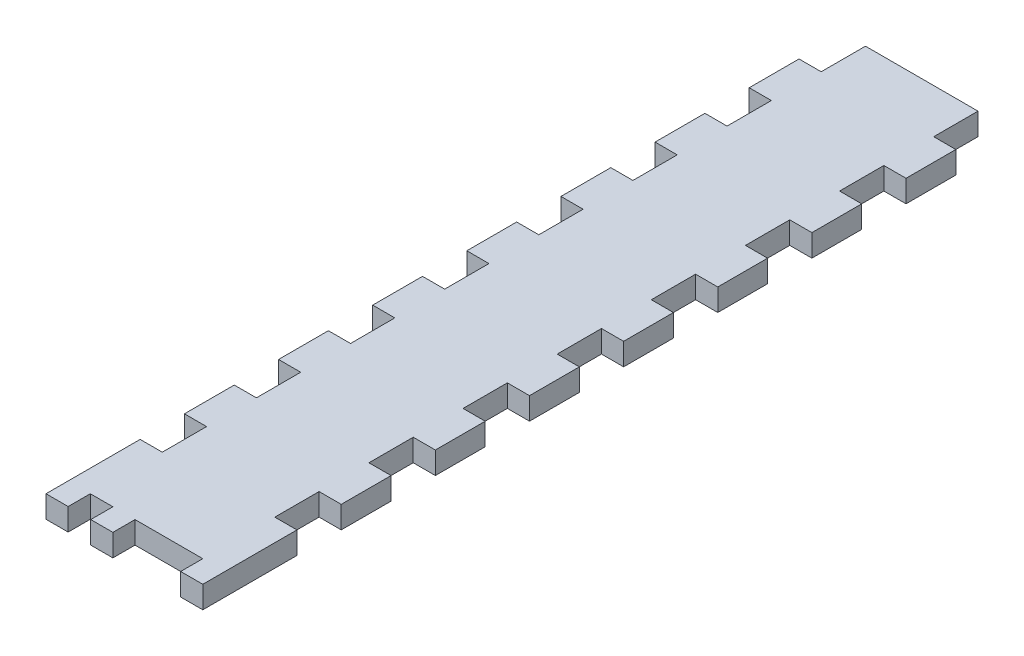
SolidWorks part; units mm, degrees
material "Acrylic (Medium-high impact)"
ref_plane "Front" through (0, 0, 0) normal (0, 0, 1) x (1, 0, 0)
ref_plane "Top" through (0, 0, 0) normal (0, 1, 0) x (1, 0, 0)
ref_plane "Right" through (0, 0, 0) normal (1, 0, 0) x (0, 0, -1)
sketch "Sketch1" plane through (0, 0, 0) normal (0, 0, 1) x (1, 0, 0)
  line L0 (0, 143.002) -> (0, -143.002) construction
  line L1 (-3.302, 133.858) -> (-3.302, -143.002)
  line L2 (-3.302, -143.002) -> (3.302, -143.002)
  line L3 (3.302, 143.002) -> (3.302, -143.002)
  line L4 (3.302, 143.002) -> (-16.256, 143.002)
  line L5 (-5.842, 136.398) -> (-16.256, 136.398)
  line L6 (-16.256, 143.002) -> (-16.256, 136.398)
  line L8 (-28.956, 155.448) -> (16.002, 155.448)
  line L9 (-28.956, 155.448) -> (-28.956, -149.352)
  line L10 (-28.956, -149.352) -> (16.002, -149.352)
  line L11 (16.002, 155.448) -> (16.002, -149.352)
  arc A0 (-3.302, 133.858) -> (-5.842, 136.398) centre (-5.842, 133.858) ccw
  point P2 (0, -143.002)
  point P11 (0, 0)
  dimension "D5" = 2.54
  dimension "D1" = 6.604
  dimension "D2" = 12.954
  dimension "D3" = 6.604
  dimension "D4" = 286.004
  dimension "D6" = 304.8
  dimension "D7" = 6.35
  dimension "D8" = 12.7
  dimension "D9" = 12.7
extrude "Boss-Extrude1" add sketch "Sketch1" along normal blind 6.35
sketch "Sketch2" plane through (16.002, 0, 0) normal (1, 0, 0) x (0, 0, -1)
  line L0 (-6.35, -149.352) -> (-6.35, 155.448) construction
  line L1 (-6.35, -47.752) -> (228.6, -47.752)
  line L2 (-6.35, -47.752) -> (-6.35, -149.352)
  line L3 (-6.35, -149.352) -> (228.6, -149.352)
  line L4 (228.6, -47.752) -> (228.6, -149.352)
  line L5 (14.4, -101.092) -> (14.4, -96.012)
  line L6 (36.4, -96.012) -> (36.4, -101.092)
  line L7 (8.4, -116.592) -> (8.4, -111.512)
  line L8 (11.4, -116.592) -> (11.4, -111.512)
  line L9 (8.4, -85.592) -> (8.4, -80.512)
  line L10 (11.4, -85.592) -> (11.4, -80.512)
  line L11 (25.4, -96.012) -> (25.4, -101.092) construction
  line L12 (42.4, -116.592) -> (42.4, -111.512)
  line L13 (39.4, -116.592) -> (39.4, -111.512)
  line L14 (39.4, -85.592) -> (39.4, -80.512)
  line L15 (42.4, -85.592) -> (42.4, -80.512)
  line L16 (0, -149.352) -> (0, 155.448) construction
  line L17 (225.425, -60.452) -> (225.425, -77.3853) construction
  line L18 (228.6, -47.752) -> (222.25, -47.752)
  line L19 (228.6, -47.752) -> (228.6, -60.452)
  line L20 (228.6, -60.452) -> (222.25, -60.452)
  line L21 (222.25, -47.752) -> (222.25, -60.452)
  line L22 (228.6, -107.0187) -> (222.25, -107.0187)
  line L23 (228.6, -107.0187) -> (228.6, -119.7187)
  line L24 (228.6, -119.7187) -> (222.25, -119.7187)
  line L25 (222.25, -107.0187) -> (222.25, -119.7187)
  line L26 (228.6, -136.652) -> (222.25, -136.652)
  line L27 (228.6, -136.652) -> (228.6, -149.352)
  line L28 (228.6, -149.352) -> (222.25, -149.352)
  line L29 (222.25, -136.652) -> (222.25, -149.352)
  line L30 (228.6, -77.3853) -> (222.25, -77.3853)
  line L31 (228.6, -77.3853) -> (228.6, -90.0853)
  line L32 (228.6, -90.0853) -> (222.25, -90.0853)
  line L33 (222.25, -77.3853) -> (222.25, -90.0853)
  line L34 (225.425, -90.0853) -> (225.425, -107.0187) construction
  line L35 (225.425, -119.7187) -> (225.425, -136.652) construction
  arc A0 (14.4, -101.092) -> (36.4, -101.092) centre (25.4, -101.092) ccw
  arc A1 (36.4, -96.012) -> (14.4, -96.012) centre (25.4, -96.012) ccw
  arc A2 (8.4, -116.592) -> (11.4, -116.592) centre (9.9, -116.592) ccw
  arc A3 (11.4, -111.512) -> (8.4, -111.512) centre (9.9, -111.512) ccw
  arc A4 (8.4, -85.592) -> (11.4, -85.592) centre (9.9, -85.592) ccw
  arc A5 (11.4, -80.512) -> (8.4, -80.512) centre (9.9, -80.512) ccw
  arc A6 (42.4, -116.592) -> (39.4, -116.592) centre (40.9, -116.592) cw
  arc A7 (39.4, -111.512) -> (42.4, -111.512) centre (40.9, -111.512) cw
  arc A8 (42.4, -85.592) -> (39.4, -85.592) centre (40.9, -85.592) cw
  arc A9 (39.4, -80.512) -> (42.4, -80.512) centre (40.9, -80.512) cw
  point P44 (25.4, -98.552)
  point P47 (-6.35, -98.552)
  line M17 (0, -149.352) -> (0, 155.448)
  line M19 (-6.35, 155.448) -> (-6.35, -149.352)
  line M20 (-6.35, -149.352) -> (0, -149.352)
  dimension "D1" = 22
  dimension "D6" = 1.5
  dimension "D10" = 1.5
  dimension "D2" = 5.08
  dimension "D3" = 5.08
  dimension "D4" = 15.5
  dimension "D5" = 15.5
  dimension "D7" = 15.5
  dimension "D8" = 15.5
  dimension "D9" = 5.08
  dimension "D11" = 25.4
  dimension "D12" = 50.8
  dimension "D13" = 203.2
  dimension "D14" = 12.7
  dimension "D15" = 6.35
extrude "Boss-Extrude2" add sketch "Sketch2" against normal blind 6.35 contours L33 L30 L4 L20 L21 L1 L3 L29 L26 L24 L25 L22 L32 A5 L10 A4 L9 A3 L8 A2 L7 A1 L6 A0 L5 L13 A7 L12 A6 L14 A9 L15 A8 M17 | L1 M19 M20 M17
sketch "Sketch3" plane through (9.652, 0, 0) normal (-1, 0, 0) x (0, 0, 1)
  line L0 (-222.25, -136.652) -> (-222.25, -149.352) construction
  line L1 (-222.25, -143.002) -> (0, -143.002)
  line L2 (-222.25, -143.002) -> (-222.25, -149.352)
  line L3 (-222.25, -149.352) -> (0, -149.352)
  line L4 (0, -143.002) -> (0, -149.352)
  dimension "D1" = 6.35
extrude "Boss-Extrude3" add sketch "Sketch3" along normal up to surface (38.608 mm away) up to face at (-28.956, 3.048, 3.175)
sketch "Sketch4" plane through (0, -149.352, 0) normal (0, -1, 0) x (1, 0, 0)
  line L0 (9.652, -20.6375) -> (9.652, -33.3375)
  line L1 (16.002, 6.35) -> (9.652, 6.35)
  line L2 (16.002, 6.35) -> (16.002, -6.35)
  line L3 (16.002, -6.35) -> (9.652, -6.35)
  line L4 (9.652, 6.35) -> (9.652, -6.35)
  line L5 (16.002, -20.6375) -> (9.652, -20.6375)
  line L6 (16.002, -20.6375) -> (16.002, -33.3375)
  line L7 (16.002, -33.3375) -> (9.652, -33.3375)
  line L8 (9.652, -47.625) -> (9.652, -60.325)
  line L9 (16.002, -47.625) -> (9.652, -47.625)
  line L10 (16.002, -47.625) -> (16.002, -60.325)
  line L11 (16.002, -60.325) -> (9.652, -60.325)
  line L12 (9.652, -74.6125) -> (9.652, -87.3125)
  line L13 (16.002, -74.6125) -> (9.652, -74.6125)
  line L14 (16.002, -74.6125) -> (16.002, -87.3125)
  line L15 (16.002, -87.3125) -> (9.652, -87.3125)
  line L16 (9.652, -101.6) -> (9.652, -114.3)
  line L17 (16.002, -101.6) -> (9.652, -101.6)
  line L18 (16.002, -101.6) -> (16.002, -114.3)
  line L19 (16.002, -114.3) -> (9.652, -114.3)
  line L20 (9.652, -128.5875) -> (9.652, -141.2875)
  line L21 (16.002, -128.5875) -> (9.652, -128.5875)
  line L22 (16.002, -128.5875) -> (16.002, -141.2875)
  line L23 (16.002, -141.2875) -> (9.652, -141.2875)
  line L24 (9.652, -155.575) -> (9.652, -168.275)
  line L25 (16.002, -155.575) -> (9.652, -155.575)
  line L26 (16.002, -155.575) -> (16.002, -168.275)
  line L27 (16.002, -168.275) -> (9.652, -168.275)
  line L28 (9.652, -182.5625) -> (9.652, -195.2625)
  line L29 (16.002, -182.5625) -> (9.652, -182.5625)
  line L30 (16.002, -182.5625) -> (16.002, -195.2625)
  line L31 (16.002, -195.2625) -> (9.652, -195.2625)
  line L32 (9.652, -209.55) -> (9.652, -222.25)
  line L33 (16.002, -209.55) -> (9.652, -209.55)
  line L34 (16.002, -209.55) -> (16.002, -222.25)
  line L35 (16.002, -222.25) -> (9.652, -222.25)
  line L36 (-6.477, 6.35) -> (-6.477, -222.25) construction
  line L37 (-28.956, 6.35) -> (16.002, 6.35) construction
  line L38 (-28.956, -222.25) -> (16.002, -222.25) construction
  line L39 (-22.606, 6.35) -> (-22.606, -222.25)
  line L40 (16.002, 6.35) -> (9.652, 6.35)
  line L41 (16.002, 6.35) -> (16.002, -222.25)
  line L42 (16.002, -222.25) -> (9.652, -222.25)
  line L43 (9.652, 6.35) -> (9.652, -222.25)
  line L44 (-28.956, -222.25) -> (-22.606, -222.25)
  line L45 (-28.956, 6.35) -> (-28.956, -222.25)
  line L46 (-28.956, 6.35) -> (-22.606, 6.35)
  line L47 (-28.956, -222.25) -> (-22.606, -222.25)
  line L48 (-28.956, -209.55) -> (-28.956, -222.25)
  line L49 (-28.956, -209.55) -> (-22.606, -209.55)
  line L50 (-22.606, -209.55) -> (-22.606, -222.25)
  line L51 (-28.956, -195.2625) -> (-22.606, -195.2625)
  line L52 (-28.956, -182.5625) -> (-28.956, -195.2625)
  line L53 (-28.956, -182.5625) -> (-22.606, -182.5625)
  line L54 (-22.606, -182.5625) -> (-22.606, -195.2625)
  line L55 (-28.956, -168.275) -> (-22.606, -168.275)
  line L56 (-28.956, -155.575) -> (-28.956, -168.275)
  line L57 (-28.956, -155.575) -> (-22.606, -155.575)
  line L58 (-22.606, -155.575) -> (-22.606, -168.275)
  line L59 (-28.956, -141.2875) -> (-22.606, -141.2875)
  line L60 (-28.956, -128.5875) -> (-28.956, -141.2875)
  line L61 (-28.956, -128.5875) -> (-22.606, -128.5875)
  line L62 (-22.606, -128.5875) -> (-22.606, -141.2875)
  line L63 (-28.956, -114.3) -> (-22.606, -114.3)
  line L64 (-28.956, -101.6) -> (-28.956, -114.3)
  line L65 (-28.956, -101.6) -> (-22.606, -101.6)
  line L66 (-22.606, -101.6) -> (-22.606, -114.3)
  line L67 (-28.956, -87.3125) -> (-22.606, -87.3125)
  line L68 (-28.956, -74.6125) -> (-28.956, -87.3125)
  line L69 (-28.956, -74.6125) -> (-22.606, -74.6125)
  line L70 (-22.606, -74.6125) -> (-22.606, -87.3125)
  line L71 (-28.956, -60.325) -> (-22.606, -60.325)
  line L72 (-28.956, -47.625) -> (-28.956, -60.325)
  line L73 (-28.956, -47.625) -> (-22.606, -47.625)
  line L74 (-22.606, -47.625) -> (-22.606, -60.325)
  line L75 (-28.956, -33.3375) -> (-22.606, -33.3375)
  line L76 (-28.956, -20.6375) -> (-28.956, -33.3375)
  line L77 (-28.956, -20.6375) -> (-22.606, -20.6375)
  line L78 (-22.606, 6.35) -> (-22.606, -6.35)
  line L79 (-28.956, -6.35) -> (-22.606, -6.35)
  line L80 (-28.956, 6.35) -> (-28.956, -6.35)
  line L81 (-28.956, 6.35) -> (-22.606, 6.35)
  line L82 (-22.606, -20.6375) -> (-22.606, -33.3375)
  line L83 (-16.129, 3.175) -> (-22.606, 3.175) construction
  line L85 (-28.956, 6.35) -> (-22.606, 6.35)
  line L86 (-28.956, 6.35) -> (-28.956, 0)
  line L87 (-28.956, 0) -> (-22.606, 0)
  line L88 (-22.606, 6.35) -> (-22.606, 0)
  line L92 (9.652, 6.35) -> (9.652, 0)
  line L93 (9.652, 6.35) -> (16.002, 6.35)
  line L94 (16.002, 6.35) -> (16.002, 0)
  line L95 (9.652, 0) -> (16.002, 0)
  line L100 (-9.652, 6.35) -> (-9.652, 0) [skipped]
  line L101 (-9.652, 0) -> (-3.302, 0) [skipped]
  line L102 (-3.302, 6.35) -> (-3.302, 0) [skipped]
  line L103 (-9.652, 6.35) -> (-3.302, 6.35) [skipped]
  line L104 (-9.779, 0) -> (-16.129, 0)
  line L105 (-9.779, 0) -> (-9.779, 6.35)
  line L106 (-9.779, 6.35) -> (-16.129, 6.35)
  line L107 (-16.129, 0) -> (-16.129, 6.35)
  line L108 (-9.779, 3.175) -> (-3.302, 3.175) construction
  line L109 (-3.302, 6.35) -> (-3.302, 0) construction
  line L110 (-22.606, 6.35) -> (-16.129, 6.35)
  line L115 (-28.956, 6.35) -> (16.002, 6.35)
  line L116 (-28.956, 6.35) -> (-28.956, 0)
  line L117 (-28.956, 0) -> (16.002, 0)
  line L118 (16.002, 6.35) -> (16.002, 0)
  line L119 (-28.956, 6.35) -> (16.002, 6.35)
  line L120 (-28.956, 6.35) -> (-28.956, 0)
  line L121 (-28.956, 0) -> (16.002, 0)
  line L122 (16.002, 6.35) -> (16.002, 0)
  line L123 (-22.606, 0) -> (-16.129, 0)
  line L124 (-9.779, 6.35) -> (9.652, 6.35)
  line L125 (-9.779, 0) -> (9.652, 0)
  line M38 (16.002, -222.25) -> (16.002, 6.35)
  line M41 (-28.956, -222.25) -> (16.002, -222.25)
  dimension "D1" = 6.35
  dimension "D2" = 12.7
  dimension "D4" = 6.35
  dimension "D5" = 6.35
  dimension "D7" = 6.35
  dimension "D3" = 9
  dimension "D6" = 3
sketch "Sketch6" plane through (0, 0, 6.35) normal (0, 0, 1) x (1, 0, 0)
  line L0 (16.002, -136.652) -> (16.002, -149.352) construction
  line L1 (16.002, -60.452) -> (9.652, -60.452)
  line L2 (16.002, -60.452) -> (16.002, -77.3853)
  line L3 (16.002, -77.3853) -> (9.652, -77.3853)
  line L4 (9.652, -60.452) -> (9.652, -77.3853)
  line L5 (16.002, -90.0853) -> (9.652, -90.0853)
  line L6 (16.002, -90.0853) -> (16.002, -107.0187)
  line L7 (16.002, -107.0187) -> (9.652, -107.0187)
  line L8 (9.652, -90.0853) -> (9.652, -107.0187)
  line L9 (16.002, -119.7187) -> (9.652, -119.7187)
  line L10 (16.002, -119.7187) -> (16.002, -136.652)
  line L11 (16.002, -136.652) -> (9.652, -136.652)
  line L12 (9.652, -119.7187) -> (9.652, -136.652)
sketch "Sketch7" plane through (16.002, 0, 0) normal (1, 0, 0) x (0, 0, -1)
  line L1 (-6.35, 180.723) -> (327.0227, 180.723)
  line L2 (-6.35, 180.723) -> (-6.35, -143.002)
  line L3 (-6.35, -143.002) -> (327.0227, -143.002)
  line L4 (327.0227, 180.723) -> (327.0227, -143.002)
  line L5 (-6.35, -149.352) -> (-6.35, 155.448) construction
  line L6 (222.25, -143.002) -> (0, -143.002) construction
  point P10 (160.3364, -143.002)
extrude "Cut-Extrude1" cut sketch "Sketch7" against normal through all
extrude "Cut-Extrude2" cut sketch "Sketch4" against normal blind 6.35 contours L7 L5 L0 M38 | L77 L45 L75 L39 | L73 L45 L71 L39 | L69 L45 L67 L39 | L65 L45 L63 L39 | L61 L45 L59 L39 | L57 L45 L55 L39 | L53 L45 L51 L39 | L49 L45 L39 M41 | L33 L32 M38 M41 | L27 L25 L24 M38 | L23 L21 L20 M38 | L19 L17 L16 M38 | L15 L13 L12 M38 | L11 L9 L8 M38 | L31 L29 L28 M38
sketch "Sketch8" plane through (0, -149.352, 0) normal (0, -1, 0) x (1, 0, 0)
  line L1 (-22.606, 6.35) -> (-16.129, 6.35)
  line L2 (-22.606, 6.35) -> (-22.606, 0)
  line L3 (-22.606, 0) -> (-16.129, 0)
  line L4 (-16.129, 6.35) -> (-16.129, 0)
  line L5 (-9.779, 6.35) -> (9.652, 6.35)
  line L6 (-9.779, 6.35) -> (-9.779, 0)
  line L7 (-9.779, 0) -> (9.652, 0)
  line L8 (9.652, 6.35) -> (9.652, 0)
extrude "Cut-Extrude4" cut sketch "Sketch8" against normal through all
